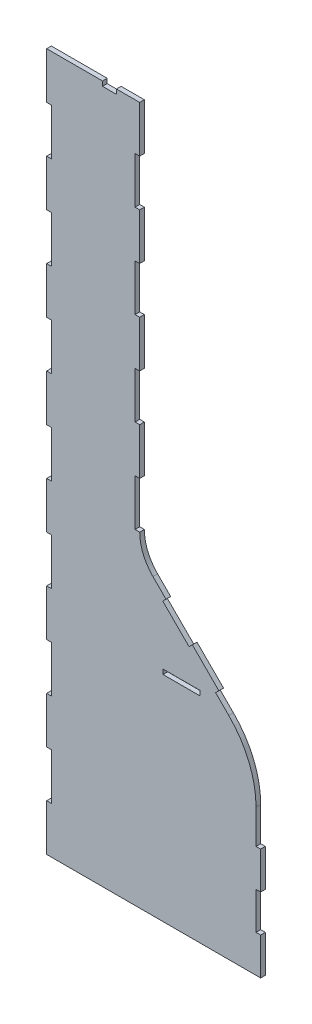
SolidWorks part; units mm, degrees
material "Contreplaqué pin"
ref_plane "Plan de face" through (0, 0, 0) normal (0, 0, 1) x (1, 0, 0)
ref_plane "Plan de dessus" through (0, 0, 0) normal (0, 1, 0) x (1, 0, 0)
ref_plane "Plan de droite" through (0, 0, 0) normal (1, 0, 0) x (0, 0, -1)
sketch "Esquisse1" plane through (0, 0, 0) normal (0, 0, 1) x (1, 0, 0)
  line L0 (100, 330) -> (128.2843, 301.7157)
  line L2 (0, 0) -> (0, 50)
  line L3 (0, 750) -> (60, 750)
  line L4 (100, 330) -> (100, 350)
  line L5 (230, 200) -> (230, 160)
  line L6 (230, 0) -> (0, 0)
  line L12 (0, 100) -> (0, 150)
  line L13 (0, 600) -> (5, 600)
  line L15 (0, 550) -> (5, 550)
  line L16 (5, 600) -> (5, 550)
  line L17 (0, 500) -> (5, 500)
  line L19 (0, 450) -> (5, 450)
  line L20 (5, 500) -> (5, 450)
  line L21 (0, 300) -> (5, 300)
  line L23 (0, 250) -> (5, 250)
  line L24 (5, 300) -> (5, 250)
  line L25 (0, 100) -> (5, 100)
  line L27 (0, 50) -> (5, 50)
  line L28 (5, 100) -> (5, 50)
  line L29 (0, 400) -> (5, 400)
  line L31 (0, 350) -> (5, 350)
  line L32 (5, 400) -> (5, 350)
  line L33 (0, 200) -> (5, 200)
  line L35 (0, 150) -> (5, 150)
  line L36 (5, 200) -> (5, 150)
  line L37 (0, 200) -> (0, 250)
  line L38 (0, 300) -> (0, 350)
  line L39 (0, 400) -> (0, 450)
  line L40 (0, 500) -> (0, 550)
  line L41 (0, 600) -> (0, 650)
  line L42 (0, 700) -> (0, 750)
  line L43 (0, 650) -> (5, 650)
  line L45 (0, 700) -> (5, 700)
  line L46 (5, 650) -> (5, 700)
  line L47 (100, 700) -> (100, 750)
  line L48 (100, 700) -> (95, 700)
  line L50 (100, 650) -> (95, 650)
  line L51 (95, 700) -> (95, 650)
  line L52 (100, 600) -> (95, 600)
  line L54 (100, 550) -> (95, 550)
  line L55 (95, 600) -> (95, 550)
  line L56 (100, 500) -> (95, 500)
  line L58 (100, 450) -> (95, 450)
  line L59 (95, 500) -> (95, 450)
  line L60 (100, 400) -> (95, 400)
  line L62 (100, 350) -> (95, 350)
  line L63 (95, 400) -> (95, 350)
  line L64 (100, 600) -> (100, 650)
  line L65 (100, 500) -> (100, 550)
  line L66 (100, 400) -> (100, 450)
  line L67 (128.2843, 301.7157) -> (124.7487, 298.1802)
  line L68 (124.7487, 298.1802) -> (153.033, 269.8959)
  line L69 (153.033, 269.8959) -> (156.5685, 273.4315)
  line L70 (156.5685, 273.4315) -> (199.9019, 230.0981)
  line L71 (214.9509, 215.0491) -> (211.4154, 211.5135)
  line L72 (211.4154, 211.5135) -> (196.3663, 226.5626)
  line L73 (196.3663, 226.5626) -> (199.9019, 230.0981)
  line L74 (214.9509, 215.0491) -> (230, 200)
  line L75 (184.8528, 245.1472) -> (169.337, 229.6314) construction
  line L76 (230, 120) -> (230, 80)
  line L77 (230, 40) -> (225, 40)
  line L79 (230, 80) -> (225, 80)
  line L80 (225, 40) -> (225, 80)
  line L81 (230, 120) -> (225, 120)
  line L83 (230, 160) -> (225, 160)
  line L84 (225, 120) -> (225, 160)
  line L85 (230, 40) -> (230, 0)
  line L87 (125, 235.1) -> (165, 235.1)
  line L88 (125, 235.1) -> (125, 230)
  line L89 (125, 230) -> (165, 230)
  line L90 (165, 235.1) -> (165, 230)
  line L94 (60, 750) -> (60, 745)
  line L95 (60, 745) -> (75, 745)
  line L96 (75, 745) -> (75, 750)
  line L97 (75, 750) -> (100, 750)
  dimension "D2" = 750
  dimension "D3" = 200
  dimension "D4" = 45
  dimension "D5" = 130
  dimension "D6" = 330
  dimension "D10" = 50
  dimension "D12" = 50
  dimension "D11" = 5
  dimension "D13" = 5
  dimension "D14" = 50
  dimension "D15" = 50
  dimension "D16" = 5
  dimension "D18" = 5
  dimension "D19" = 120
  dimension "D20" = 63.8478
  dimension "D21" = 21.2826
  dimension "D22" = 21.2826
  dimension "D17" = 40
  dimension "D23" = 40
  dimension "D24" = 5
  dimension "D26" = 5.1
  dimension "D27" = 25
  dimension "D28" = 40
  dimension "D29" = 100
  dimension "D25" = 40
  dimension "D7" = 60
  dimension "D9" = 100
  dimension "D8" = 15
  dimension "D30" = 5
extrude "Boss.-Extru.1" add sketch "Esquisse1" along normal blind 5
sketch "Esquisse3" plane through (0, 0, 5) normal (0, 0, 1) x (1, 0, 0)
  line L4 (211.4154, 211.5135) -> (196.3663, 226.5626) construction
  line L6 (225, 120) -> (225, 160) construction
  line L10 (225, 156.5076) -> (230, 156.5076)
  line L11 (230, 156.5076) -> (230, 200)
  line L12 (230, 160) -> (230, 200) construction
  line L13 (195.7107, 227.2183) -> (181.5685, 241.3604)
  line L14 (181.5685, 241.3604) -> (185.1041, 244.8959)
  line L15 (185.1041, 244.8959) -> (230, 200)
  line L16 (199.9019, 230.0981) -> (156.5685, 273.4315) construction
  arc A0 (225, 156.5076) -> (195.7107, 227.2183) centre (125, 156.5076) ccw
  dimension "D1" = 100
  dimension "D2" = 20
extrude "Enlèv. mat.-Extru.1" cut sketch "Esquisse3" against normal up to next
sketch "Esquisse4" plane through (0, 0, 5) normal (0, 0, 1) x (1, 0, 0)
  line L0 (100, 330) -> (100, 350) construction
  line L1 (128.2843, 301.7157) -> (100, 330) construction
  line L2 (100, 350) -> (100, 330)
  line L3 (100, 330) -> (114.1421, 315.8579)
  arc A0 (114.1421, 315.8579) -> (100, 350) centre (148.2843, 350) cw
extrude "Boss.-Extru.2" add sketch "Esquisse4" against normal blind 5
equation "\"D21@Esquisse1\"=\"D20@Esquisse1\"/3"
equation "\"D22@Esquisse1\"=\"D20@Esquisse1\"/3"
equation "\"D17@Esquisse1\"=\"D19@Esquisse1\"/3"
equation "\"D23@Esquisse1\"=\"D19@Esquisse1\"/3"
